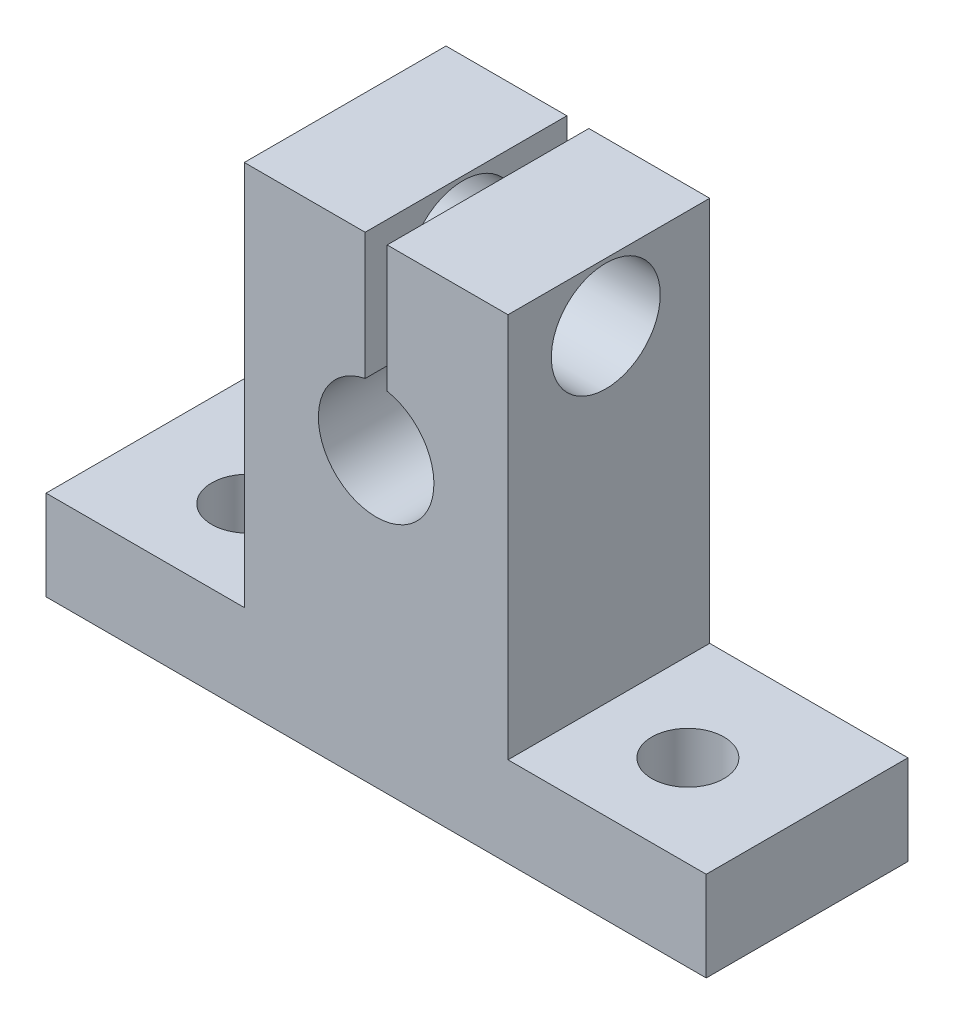
SolidWorks part; units mm, degrees
ref_plane "Front Plane" through (0, 0, 0) normal (0, 0, 1) x (1, 0, 0)
ref_plane "Top Plane" through (0, 0, 0) normal (0, 1, 0) x (1, 0, 0)
ref_plane "Right Plane" through (0, 0, 0) normal (1, 0, 0) x (0, 0, -1)
sketch "Sketch1" plane through (0, 0, 0) normal (0, 0, 1) x (1, 0, 0)
  line L1 (-9.1313, -16.4592) -> (9.1313, -16.4592)
  line L2 (-9.1313, -16.4592) -> (-9.1313, 16.4592)
  line L3 (-9.1313, 16.4592) -> (9.1313, 16.4592)
  line L4 (9.1313, -16.4592) -> (9.1313, 16.4592)
  line L5 (-9.1313, -16.4592) -> (9.1313, 16.4592) construction
  line L6 (-9.1313, 16.4592) -> (9.1313, -16.4592) construction
  point P0 (0, 0)
  dimension "D1" = 18.2626
  dimension "D2" = 32.9184
extrude "Main Body]" add sketch "Sketch1" along normal blind 13.97
sketch "Sketch2" plane through (0, 0, 13.97) normal (0, 0, 1) x (1, 0, 0)
  line L0 (-9.1313, -16.4592) -> (9.1313, -16.4592) construction
  line L5 (-22.86, -10.2362) -> (22.86, -10.2362)
  line L6 (-22.86, -10.2362) -> (-22.86, -16.4592)
  line L7 (-22.86, -16.4592) -> (22.86, -16.4592)
  line L9 (22.86, -10.2362) -> (22.86, -16.4592)
  line L10 (-22.86, -10.2362) -> (22.86, -16.4592) construction
  line L11 (-22.86, -16.4592) -> (22.86, -10.2362) construction
  point P0 (0, -13.3477)
  point P5 (0, -10.2362)
  dimension "D1" = 45.72
  dimension "D2" = 6.223
extrude "Bottom Body" add sketch "Sketch2" against normal blind 13.97
sketch "Sketch3" plane through (0, 0, 13.97) normal (0, 0, 1) x (1, 0, 0)
  line L5 (9.1313, 16.4592) -> (-9.1313, 16.4592) construction
  circle A0 centre (0, 3.7592) radius 4.0005
  dimension "D1" = 8.001
  dimension "D3" = 12.7
extrude "Center Hole" cut sketch "Sketch3" against normal through all both and the other way through all
sketch "Sketch4" plane through (0, 0, 13.97) normal (0, 0, 1) x (1, 0, 0)
  line L5 (9.1313, 16.4592) -> (-9.1313, 16.4592) construction
  line L6 (-0.762, 28.4904) -> (0.762, 28.4904)
  line L7 (-0.762, 28.4904) -> (-0.762, 4.428)
  line L8 (-0.762, 4.428) -> (0.762, 4.428)
  line L9 (0.762, 28.4904) -> (0.762, 4.428)
  line L10 (-0.762, 28.4904) -> (0.762, 4.428) construction
  line L11 (-0.762, 4.428) -> (0.762, 28.4904) construction
  point P0 (0, 16.4592)
  dimension "D1" = 1.524
  dimension "D2" = 24.0625
extrude "Center Cut" cut sketch "Sketch4" against normal through all
sketch "Sketch5" plane through (9.1313, 0, 0) normal (1, 0, 0) x (0, 0, -1)
  line L0 (-13.97, 16.4592) -> (0, 16.4592) construction
  circle A0 centre (-7.1968, 12.3952) radius 3.7719
  dimension "D1" = 7.5438
  dimension "D2" = 4.064
extrude "Side Hole" cut sketch "Sketch5" against normal through all
hole_wizard "Ø5.0mm Dowel Hole1" positions "Sketch9" profile "Sketch10" hole size "Ø5.0" standard "ANSI Metric" end condition through all
sketch "Sketch9" plane through (0, -10.2362, 0) normal (0, 1, 0) x (1, 0, 0)
  line L0 (22.86, -13.97) -> (9.1313, -13.97) construction
  point P0 (15.24, -7.62)
  dimension "D1" = 15.24
  dimension "D2" = 6.35
sketch "Sketch10" plane through (15.24, -10.2362, 7.62) normal (1, 0, 0) x (0, 0, 1)
  line L0 (0, 0) -> (0, 6.223)
  line L1 (0, 6.223) -> (2.5, 6.223)
  line L2 (2.5, 6.223) -> (2.5, 0)
  line L5 (2.5, 0) -> (0, 0)
  line L11 (0, -6.35) -> (0, 107.95) construction
  dimension "Thru Hole Dia." = 5
  dimension "Thru Hole Depth" = 6.223
mirror "Mirror1" about plane through (0, 0, 0) normal (1, 0, 0) of "Ø5.0mm Dowel Hole1"
